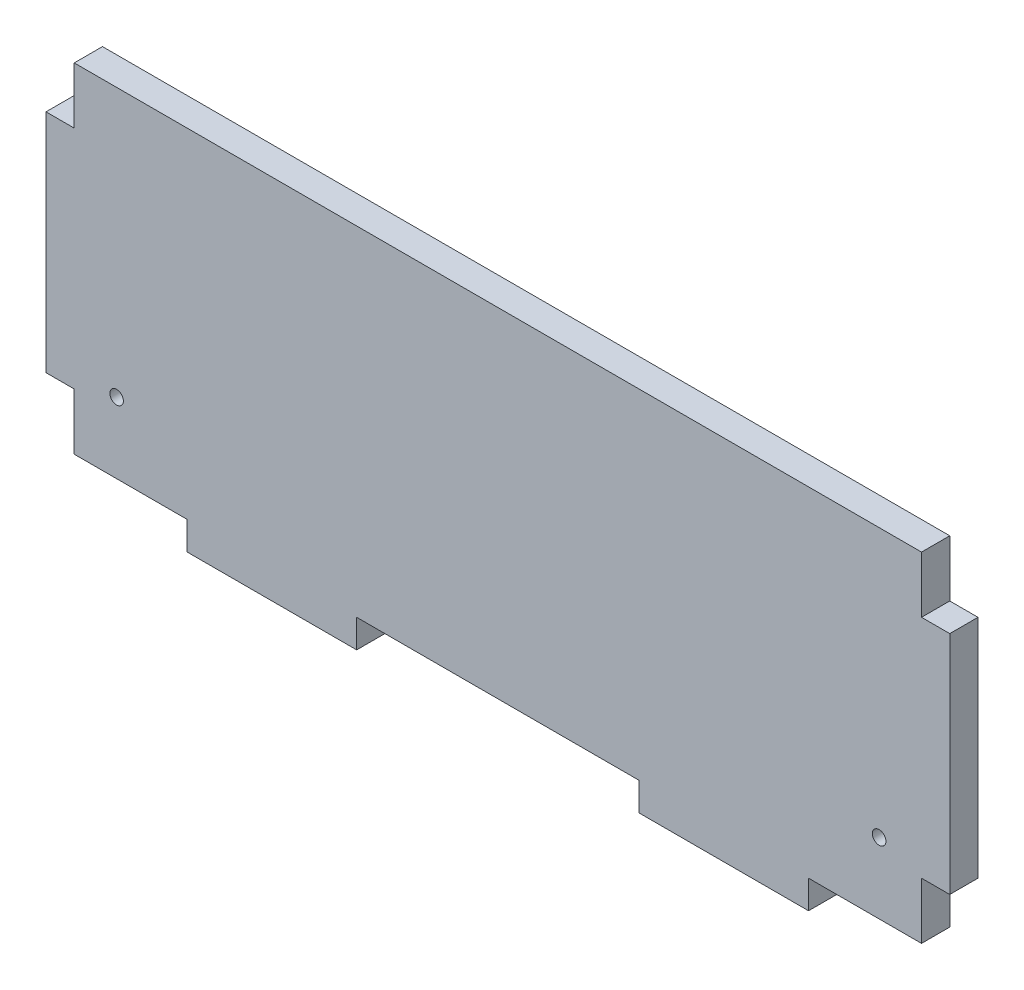
SolidWorks part; units mm, degrees
ref_plane "Front Plane" through (0, 0, 0) normal (0, 0, 1) x (1, 0, 0)
ref_plane "Top Plane" through (0, 0, 0) normal (0, 1, 0) x (1, 0, 0)
ref_plane "Right Plane" through (0, 0, 0) normal (1, 0, 0) x (0, 0, -1)
sketch "Sketch1" plane through (0, 0, 0) normal (0, 0, 1) x (1, 0, 0)
  line L1 (-95.25, -38.1) -> (95.25, -38.1)
  line L2 (-95.25, -38.1) -> (-95.25, 38.1)
  line L3 (-95.25, 38.1) -> (95.25, 38.1)
  line L4 (95.25, -38.1) -> (95.25, 38.1)
  line L5 (-95.25, -38.1) -> (95.25, 38.1) construction
  line L6 (-95.25, 38.1) -> (95.25, -38.1) construction
  point P0 (0, 0)
  dimension "D1" = 190.5
  dimension "D2" = 76.2
extrude "Boss-Extrude1" add sketch "Sketch1" along normal blind 6.35
sketch "Sketch2" plane through (-95.25, 0, 0) normal (-1, 0, 0) x (0, 0, 1)
  line L0 (0, 38.1) -> (0, -38.1) construction
  line L1 (0, 25.4) -> (6.35, 25.4)
  line L2 (0, 25.4) -> (0, -25.4)
  line L3 (0, -25.4) -> (6.35, -25.4)
  line L4 (6.35, 25.4) -> (6.35, -25.4)
  line L5 (6.35, 38.1) -> (6.35, -38.1) construction
  line L6 (6.35, 38.1) -> (0, 38.1) construction
  line L7 (6.35, -38.1) -> (0, -38.1) construction
  dimension "D1" = 12.7
  dimension "D2" = 12.7
extrude "Boss-Extrude2" add sketch "Sketch2" along normal blind 6.35
sketch "Sketch3" plane through (95.25, 0, 0) normal (1, 0, 0) x (0, 0, -1)
  line L0 (-6.35, -38.1) -> (-6.35, 38.1) construction
  line L1 (-6.35, 25.4) -> (0, 25.4)
  line L2 (-6.35, 25.4) -> (-6.35, -25.4)
  line L3 (-6.35, -25.4) -> (0, -25.4)
  line L4 (0, 25.4) -> (0, -25.4)
  line L5 (0, -38.1) -> (0, 38.1) construction
  line L6 (-6.35, 38.1) -> (0, 38.1) construction
  line L7 (-6.35, -38.1) -> (0, -38.1) construction
  dimension "D1" = 12.7
  dimension "D2" = 12.7
extrude "Boss-Extrude3" add sketch "Sketch3" along normal blind 6.35
sketch "Sketch4" plane through (0, -38.1, 0) normal (0, -1, 0) x (1, 0, 0)
  line L0 (-95.25, 6.35) -> (95.25, 6.35) construction
  line L1 (-69.85, 6.35) -> (-31.75, 6.35)
  line L2 (-69.85, 6.35) -> (-69.85, 0)
  line L3 (-69.85, 0) -> (-31.75, 0)
  line L4 (-31.75, 6.35) -> (-31.75, 0)
  line L5 (-95.25, 0) -> (95.25, 0) construction
  line L6 (-95.25, 6.35) -> (-95.25, 0) construction
  line L7 (31.75, 6.35) -> (69.85, 6.35)
  line L8 (31.75, 6.35) -> (31.75, 0)
  line L9 (31.75, 0) -> (69.85, 0)
  line L10 (69.85, 6.35) -> (69.85, 0)
  line L11 (95.25, 6.35) -> (95.25, 0) construction
  point P14 (95.25, 3.175)
  dimension "D1" = 25.4
  dimension "D2" = 25.4
  dimension "D3" = 38.1
  dimension "D4" = 38.1
extrude "Boss-Extrude4" add sketch "Sketch4" along normal blind 6.35
sketch "Sketch5" plane through (0, 0, 6.35) normal (0, 0, 1) x (1, 0, 0)
  line L0 (82.55, -31.75) -> (82.55, -38.1) construction
  line L1 (69.85, -38.1) -> (95.25, -38.1) construction
  line L2 (95.25, -38.1) -> (95.25, -25.4) construction
  line L3 (85.09, -29.21) -> (85.09, -38.1)
  line L4 (80.01, -29.21) -> (80.01, -38.1)
  circle A0 centre (82.55, -29.21) radius 2.54
  dimension "D2" = 5.08
  dimension "D1" = 6.35
  dimension "D3" = 12.7
extrude "Cut-Extrude3" [suppressed] cut sketch "Sketch5" against normal through all
extrude "Cut-Extrude4" cut sketch "Sketch6" against normal blind 6.35
sketch "Sketch6" plane through (23.7637, 98.5857, 0) normal (0, 0, -1) x (-1, 0, 0)
  circle A0 centre (-61.9613, -120.8107) radius 1.524
  circle A2 centre (109.4887, -120.8107) radius 1.524
